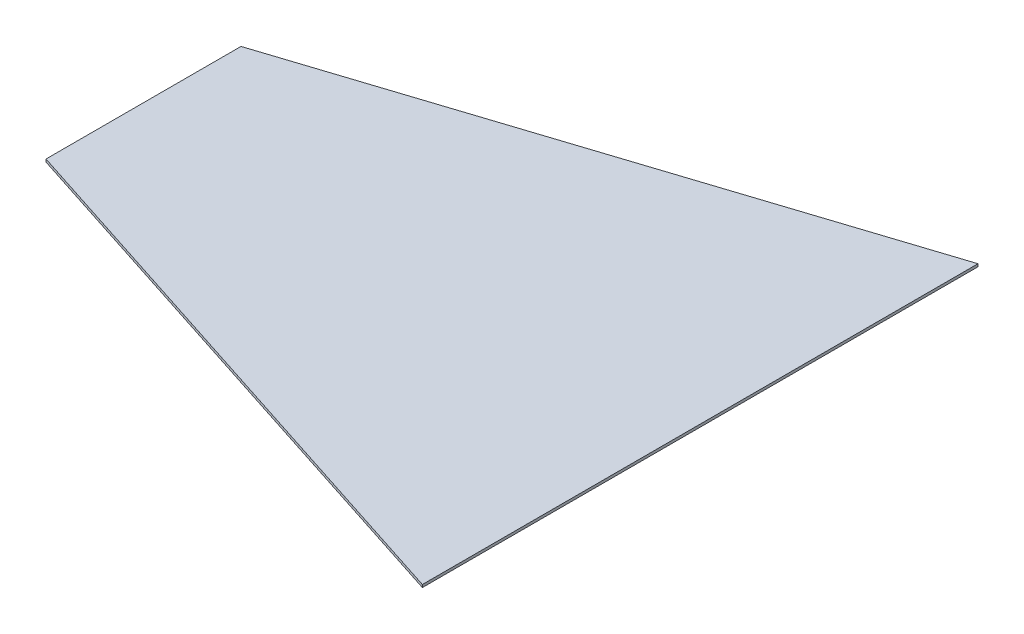
SolidWorks part; units mm, degrees
ref_plane "Front Plane" through (0, 0, 0) normal (0, 0, 1) x (1, 0, 0)
ref_plane "Top Plane" through (0, 0, 0) normal (0, 1, 0) x (1, 0, 0)
ref_plane "Right Plane" through (0, 0, 0) normal (1, 0, 0) x (0, 0, -1)
sketch "Sketch1" plane through (0, 0, 0) normal (0, 1, 0) x (1, 0, 0)
  line L1 (-232.9232, 61.4747) -> (296.4128, 61.4747)
  line L2 (-232.9232, 61.4747) -> (-232.9232, -466.8453)
  line L3 (-232.9232, -466.8453) -> (296.4128, -466.8453)
  line L4 (296.4128, 61.4747) -> (296.4128, -466.8453)
  dimension "D1" = 529.336
  dimension "D2" = 528.32
extrude "Boss-Extrude1" add sketch "Sketch1" along normal blind 2.54
sketch "Sketch2" plane through (0, 2.54, 0) normal (0, 1, 0) x (1, 0, 0)
  line L0 (296.4128, -466.8453) -> (-232.9232, -295.3953)
  line L2 (-232.9232, 61.4747) -> (-232.9232, -466.8453) construction
  line L3 (-232.9232, -295.3953) -> (-232.9232, -466.8453)
  line L4 (-232.9232, -466.8453) -> (296.4128, -466.8453)
  line L5 (296.4128, 61.4747) -> (-232.9232, -109.9753)
  line L6 (-232.9232, -109.9753) -> (-232.9232, 61.4747)
  line L7 (296.4128, 61.4747) -> (-232.9232, 61.4747) construction
  line L8 (-232.9232, 61.4747) -> (296.4128, 61.4747)
  dimension "D1" = 171.45
  dimension "D2" = 171.45
extrude "Cut-Extrude1" cut sketch "Sketch2" against normal blind 2.54
